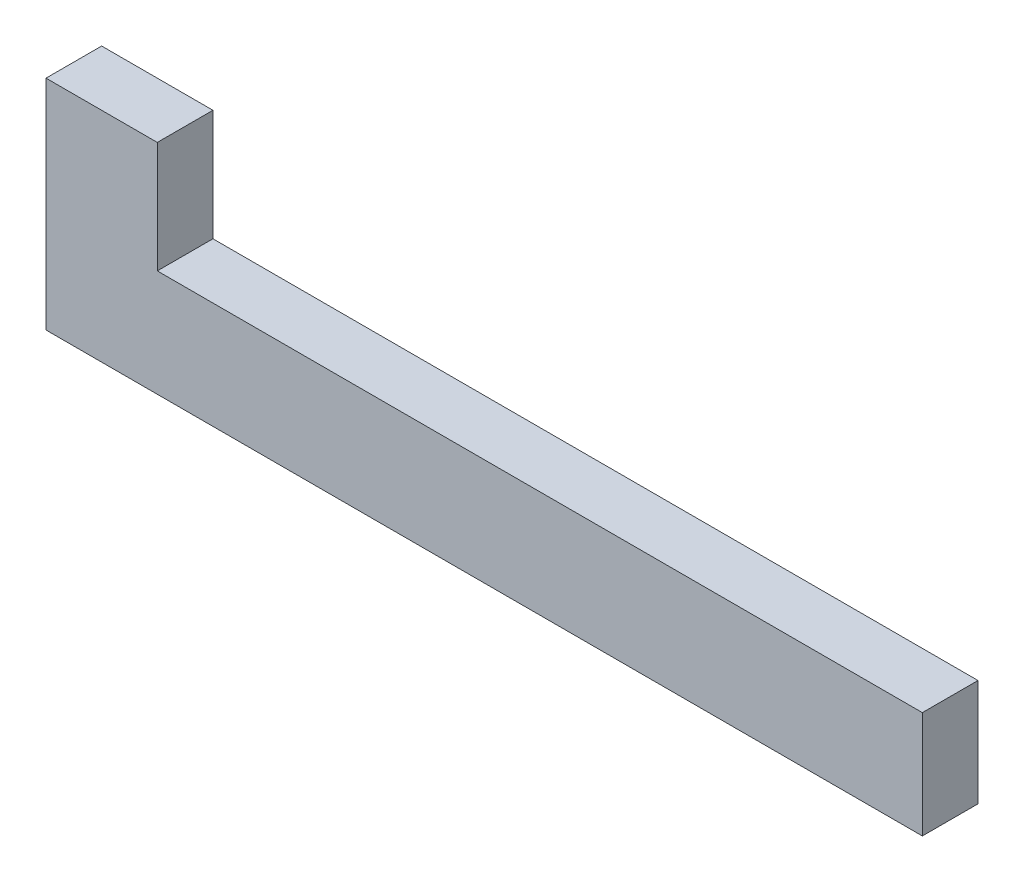
SolidWorks part; units mm, degrees
ref_plane "Front Plane" through (0, 0, 0) normal (0, 0, 1) x (1, 0, 0)
ref_plane "Top Plane" through (0, 0, 0) normal (0, 1, 0) x (1, 0, 0)
ref_plane "Right Plane" through (0, 0, 0) normal (1, 0, 0) x (0, 0, -1)
sketch "Sketch1" plane through (0, 0, 0) normal (0, 1, 0) x (1, 0, 0)
  line L1 (-25, 1.5875) -> (25, 1.5875)
  line L2 (-25, 1.5875) -> (-25, -1.5875)
  line L3 (-25, -1.5875) -> (25, -1.5875)
  line L4 (25, 1.5875) -> (25, -1.5875)
  line L5 (-25, 1.5875) -> (25, -1.5875) construction
  line L6 (-25, -1.5875) -> (25, 1.5875) construction
  point P0 (0, 0)
  dimension "D1" = 3.175
  dimension "D2" = 50
extrude "Boss-Extrude1" add sketch "Sketch1" along normal blind 6.096
sketch "Sketch2" plane through (0, 0, -1.5875) normal (0, 0, -1) x (-1, 0, 0)
  line L1 (25, 6.096) -> (18.65, 6.096)
  line L2 (25, 6.096) -> (25, 12.446)
  line L3 (25, 12.446) -> (18.65, 12.446)
  line L4 (18.65, 6.096) -> (18.65, 12.446)
  dimension "D1" = 6.35
  dimension "D2" = 6.35
extrude "Boss-Extrude2" add sketch "Sketch2" against normal up to surface (3.175 mm away) up to face at (0, 3.048, 1.5875)
